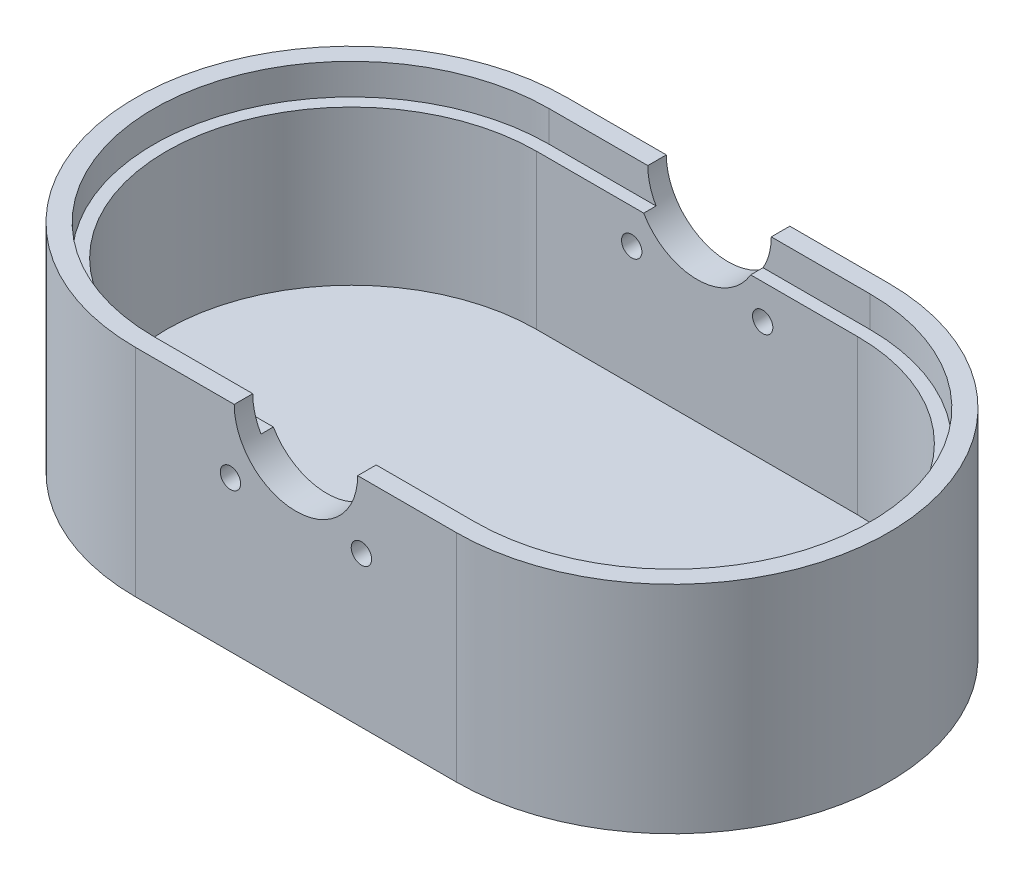
SolidWorks part; units mm, degrees
ref_plane "정면" through (0, 0, 0) normal (0, 0, 1) x (1, 0, 0)
ref_plane "윗면" through (0, 0, 0) normal (0, 1, 0) x (1, 0, 0)
ref_plane "우측면" through (0, 0, 0) normal (1, 0, 0) x (0, 0, -1)
sketch "스케치1" plane through (0, 0, 0) normal (0, 1, 0) x (1, 0, 0)
  line L0 (0, 0) -> (50000, 0) construction
  line L1 (-26, 35) -> (26, 35)
  line L3 (-26, -35) -> (26, -35)
  arc A0 (-26, 35) -> (-26, -35) centre (-26, 0) ccw
  arc A2 (26, -35) -> (26, 35) centre (26, 0) ccw
  point P0 (0, 0)
  dimension "D3" = 70
  dimension "D1" = 52
  dimension "D2" = 70
extrude "보스-돌출1" add sketch "스케치1" along normal blind 35
sketch "스케치2" plane through (0, 35, 0) normal (0, 1, 0) x (1, 0, 0)
  line L4 (26, 30) -> (-26, 30)
  line L5 (-26, -30) -> (26, -30)
  line L6 (26, 30) -> (-26, 30)
  line L7 (-26, -30) -> (26, -30)
  arc A4 (26, -30) -> (26, 30) centre (26, 0) ccw
  arc A5 (-26, 30) -> (-26, -30) centre (-26, 0) ccw
  arc A6 (26, -30) -> (26, 30) centre (26, 0) ccw
  arc A7 (-26, 30) -> (-26, -30) centre (-26, 0) ccw
  dimension "D1" = 5
extrude "컷-돌출1" cut sketch "스케치2" against normal blind 30
sketch "스케치3" plane through (0, 0, 35) normal (0, 0, 1) x (1, 0, 0)
  line L0 (0, 0) -> (0, 50000) construction
  line L1 (-26, 35) -> (26, 35) construction
  line L2 (0, 35) -> (35355.3391, 35390.3391) construction
  line L3 (0, 35) -> (-35355.3391, 35390.3391) construction
  line L4 (56, 35) -> (26, 35) construction
  circle A0 centre (0, 35) radius 10
  circle A1 centre (0, 35) radius 15 construction
  circle A2 centre (10.6066, 24.3934) radius 2 construction
  circle A3 centre (-10.6066, 24.3934) radius 2 construction
  dimension "D1" = 20
  dimension "D2" = 30
  dimension "D4" = 4
  dimension "D5" = 4
  dimension "D3" = 45
extrude "컷-돌출2" cut sketch "스케치3" against normal through all both and the other way through all
sketch "스케치4" plane through (0, 35, 0) normal (0, 1, 0) x (1, 0, 0)
  line L6 (-26, -32) -> (26, -32)
  line L7 (26, 32) -> (-26, 32)
  line L9 (-26, -30) -> (26, -30)
  line L12 (26, 30) -> (-26, 30)
  line L13 (-26, -30) -> (26, -30)
  line L14 (26, 30) -> (-26, 30)
  arc A4 (-26, 32) -> (-26, -32) centre (-26, 0) ccw
  arc A5 (26, -32) -> (26, 32) centre (26, 0) ccw
  arc A15 (26, -30) -> (26, 30) centre (26, 0) ccw
  arc A16 (-26, 30) -> (-26, -30) centre (-26, 0) ccw
  arc A17 (26, -30) -> (26, 30) centre (26, 0) ccw
  arc A18 (-26, 30) -> (-26, -30) centre (-26, 0) ccw
  dimension "D1" = 0
extrude "컷-돌출3" cut sketch "스케치4" against normal blind 5
hole_wizard "M4 나사 구멍1" positions "스케치5" profile "스케치6" tap size "M4" standard "ISO" end condition up to next
sketch "스케치5" plane through (0, 0, 35) normal (0, 0, 1) x (1, 0, 0)
  point P0 (-10.6066, 24.3934)
  point P3 (10.6066, 24.3934)
sketch "스케치6" plane through (-10.6066, 24.3934, 35) normal (1, 0, 0) x (0, -1, 0)
  line L0 (0, 0) -> (0, 5)
  line L1 (0, 5) -> (1.65, 5)
  line L2 (1.65, 5) -> (1.65, 0)
  line L5 (1.65, 0) -> (0, 0)
  line L11 (0, -6.35) -> (0, 107.95) construction
  dimension "관통 탭 드릴 지름" = 3.3
  dimension "관통 탭 드릴 깊이" = 5
cosmetic thread "구멍 나사산1" parameters "D2"=4
cosmetic thread "구멍 나사산2" parameters "D2"=4
hole_wizard "M4 나사 구멍2" positions "스케치7" profile "스케치8" tap size "M4" standard "ISO" end condition up to next
sketch "스케치7" plane through (0, 0, -35) normal (0, 0, -1) x (-1, 0, 0)
  point P2 (-10.6066, 24.3934)
  point P5 (10.6066, 24.3934)
  point P9 (0, 0)
sketch "스케치8" plane through (10.6066, 24.3934, -35) normal (1, 0, 0) x (0, 1, 0)
  line L0 (0, 0) -> (0, 5)
  line L1 (0, 5) -> (1.65, 5)
  line L2 (1.65, 5) -> (1.65, 0)
  line L5 (1.65, 0) -> (0, 0)
  line L11 (0, -6.35) -> (0, 107.95) construction
  dimension "관통 탭 드릴 지름" = 3.3
  dimension "관통 탭 드릴 깊이" = 5
cosmetic thread "구멍 나사산3" parameters "D2"=4
cosmetic thread "구멍 나사산4" parameters "D2"=4
